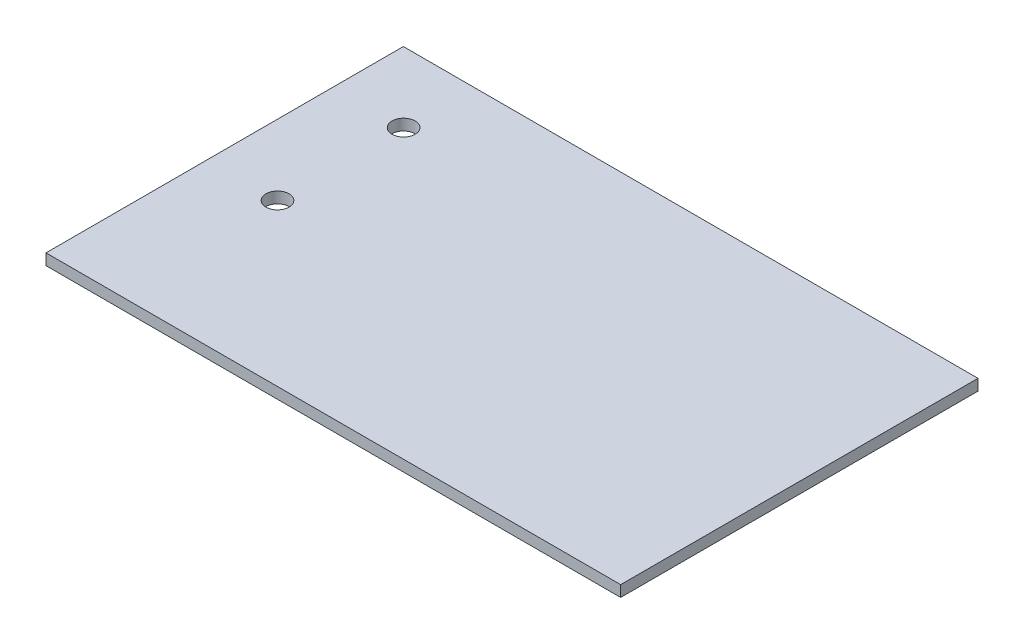
SolidWorks part; units mm, degrees
material "ABS"
ref_plane "Front Plane" through (0, 0, 0) normal (0, 0, 1) x (1, 0, 0)
ref_plane "Top Plane" through (0, 0, 0) normal (0, 1, 0) x (1, 0, 0)
ref_plane "Right Plane" through (0, 0, 0) normal (1, 0, 0) x (0, 0, -1)
sketch "Sketch1" plane through (0, 0, 0) normal (0, 1, 0) x (1, 0, 0)
  line L1 (0, 0) -> (82, 0)
  line L2 (0, 0) -> (0, 50.9916)
  line L3 (0, 50.9916) -> (82, 50.9916)
  line L4 (82, 0) -> (82, 50.9916)
  dimension "D1" = 82
extrude "Boss-Extrude1" add sketch "Sketch1" along normal blind 1.5875
sketch "Sketch2" plane through (0, 1.5875, 0) normal (0, 1, 0) x (1, 0, 0)
  line L0 (82, 50.9916) -> (0, 50.9916) construction
  line L1 (0, 50.9916) -> (0, 0) construction
  circle A0 centre (10.04, 40.9916) radius 1.65
  circle A1 centre (10.04, 22.9916) radius 1.65
  dimension "D1" = 3.3
  dimension "D2" = 10
  dimension "D3" = 10.04
  dimension "D4" = 18
extrude "Cut-Extrude1" cut sketch "Sketch2" against normal blind 10
